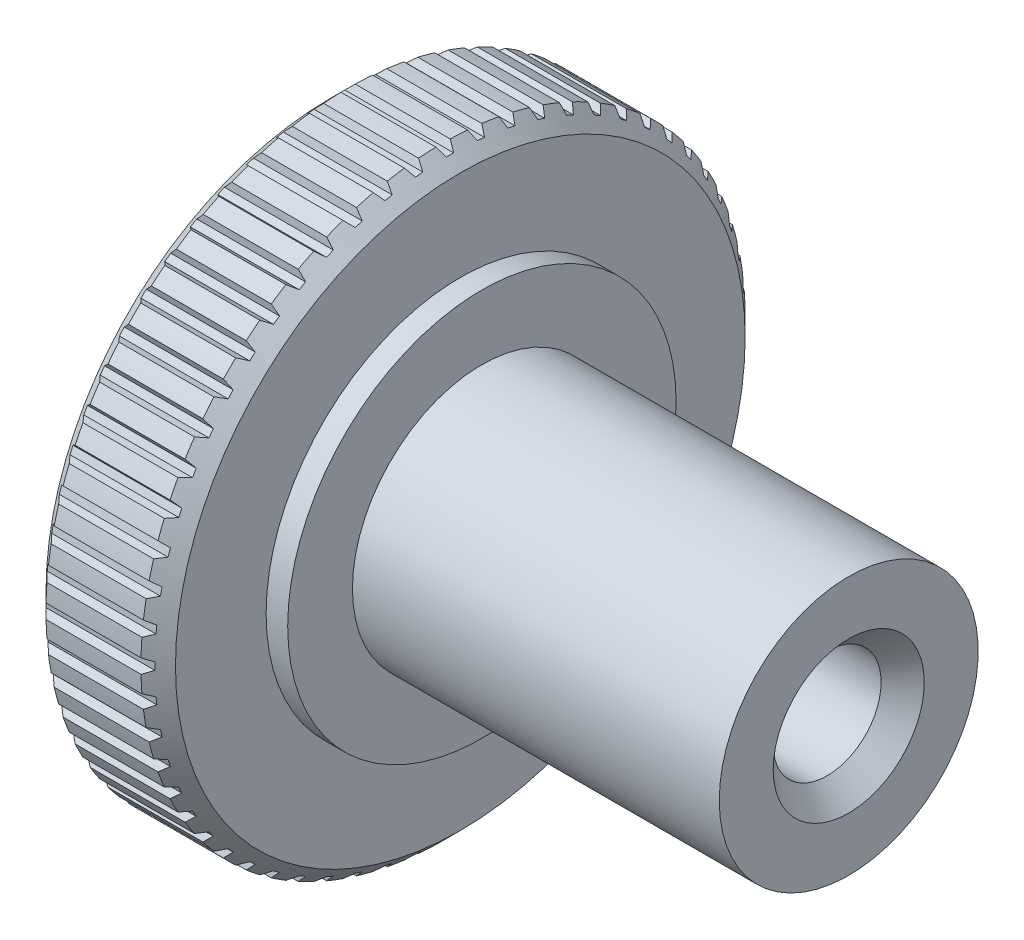
SolidWorks part; units mm, degrees
ref_plane "Front" through (0, 0, 0) normal (0, 0, 1) x (1, 0, 0)
ref_plane "Top" through (0, 0, 0) normal (0, 1, 0) x (1, 0, 0)
ref_plane "Right" through (0, 0, 0) normal (1, 0, 0) x (0, 0, -1)
sketch "Sketch1" plane through (0, 0, 0) normal (0, 0, 1) x (1, 0, 0)
  line L0 (-16.1137, 0) -> (18.4833, 0) construction
  line L1 (12, 0) -> (12, 3)
  line L2 (12, 3) -> (3.5, 3)
  line L5 (3.5, 3) -> (3.5, 4.5)
  line L6 (3.5, 4.5) -> (3, 4.5)
  line L7 (3, 4.5) -> (3, 7)
  line L8 (3, 7) -> (0, 7)
  line L9 (0, 7) -> (0, 0)
  line L10 (0, 0) -> (12, 0)
  dimension "D1" = 9
  dimension "D2" = 6
  dimension "D4" = 8.5
  dimension "D5" = 0.5
  dimension "D6" = 3
  dimension "D7" = 14
revolve "Revolve1" add sketch "Sketch1" angle 360 about L0
chamfer "Chamfer1" distance 0.4 angle 45 2 edges at (3, 0, 7) (0, 0, 7)
sketch "Sketch5" plane through (0, 0, 0) normal (-1, 0, 0) x (0, 0, 1)
  line L0 (0.1554, 6.361) -> (0, 6.67) construction
  line L1 (0, -55) -> (0, 55) construction
  line L2 (0, 6.67) -> (-0.1554, 6.361) construction
  line L3 (-0.1554, 6.361) -> (0.1554, 6.361) construction
  line L4 (-0.085, 6.839) -> (0.085, 6.839)
  line L5 (0.085, 6.839) -> (0.165, 6.9981)
  line L6 (-0.165, 6.9981) -> (-0.085, 6.839)
  arc A1 (-0.165, 6.9981) -> (0.165, 6.9981) centre (0, 0) cw
  circle A2 centre (0, 0) radius 7 construction
  point P4 (0, 6.361)
  point P12 (0, 7)
  dimension "D1" = 0.33
  dimension "D2" = 0.33
  dimension "D3" = 0.161
extrude "Cut-Extrude1" cut sketch "Sketch5" against normal up to surface (3 mm away) up to face at (3, 0, 6.6)
pattern_circular "CirPattern1" count 60 over 360 about axis through (0, 0, 0) along (1, 0, 0) of "Cut-Extrude1"
sketch "Sketch6" plane through (12, 0, 0) normal (1, 0, 0) x (0, 0, -1)
  circle A0 centre (0, 0) radius 1.25
  dimension "D1" = 2.5
extrude "Cut-Extrude2" cut sketch "Sketch6" against normal through all
chamfer "Chamfer2" distance 0.5 angle 45 2 edges at (0, 0, -1.25) (12, 0, -1.25)
